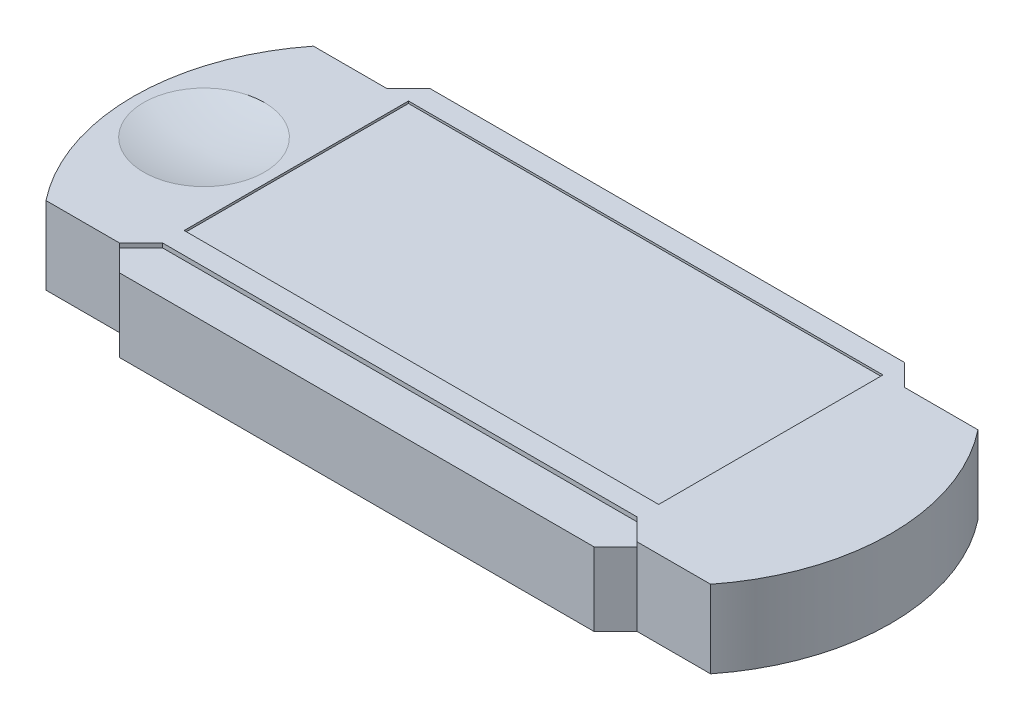
SolidWorks part; units mm, degrees
ref_plane "Front Plane" through (0, 0, 0) normal (0, 0, 1) x (1, 0, 0)
ref_plane "Top Plane" through (0, 0, 0) normal (0, 1, 0) x (1, 0, 0)
ref_plane "Right Plane" through (0, 0, 0) normal (1, 0, 0) x (0, 0, -1)
sketch "Sketch1" plane through (0, 0, 0) normal (0, 1, 0) x (1, 0, 0)
  line L0 (-87.8, 0) -> (87.8, 0) construction
  line L1 (-55, -36) -> (55, -36)
  line L2 (55, -36) -> (60, -31)
  line L3 (60, -31) -> (77.0301, -31)
  line L4 (0, 37.4833) -> (0, -47.1914) construction
  line L5 (60, 31) -> (77.0301, 31)
  line L6 (55, 36) -> (60, 31)
  line L7 (-55, 36) -> (55, 36)
  line L8 (-55, 36) -> (-60, 31)
  line L9 (-60, 31) -> (-77.0301, 31)
  line L10 (-60, -31) -> (-77.0301, -31)
  line L11 (-55, -36) -> (-60, -31)
  arc A0 (77.0301, -31) -> (77.0301, 31) centre (37.8, 0) ccw
  arc A1 (-77.0301, -31) -> (-77.0301, 31) centre (-37.8, 0) cw
  point P29 (0, 36)
  point P32 (0, -36)
  dimension "D5" = 50
  dimension "D1" = 72
  dimension "D2" = 62
  dimension "D3" = 110
  dimension "D4" = 45
  dimension "D6" = 75.6
extrude "Boss-Extrude1" add sketch "Sketch1" against normal blind 18
sketch "Sketch2" plane through (0, 0, 0) normal (0, 1, 0) x (1, 0, 0)
  line L0 (55, -36) -> (60, -31) construction
  line L1 (-55, -36) -> (55, -36) construction
  line L2 (-60, -31) -> (-55, -36) construction
  line L3 (55, -36) -> (60, -31)
  line L4 (-55, -36) -> (55, -36)
  line L5 (-60, -31) -> (-55, -36)
  line L6 (-60, -31) -> (60, -31) construction
  line L7 (-60, -31) -> (-55, -26)
  line L8 (-55, -26) -> (55, -26)
  line L9 (55, -26) -> (60, -31)
extrude "Cut-Extrude1" cut sketch "Sketch2" against normal blind 1
sketch "Sketch3" plane through (0, 0, 0) normal (0, 1, 0) x (1, 0, 0)
  line L0 (-60, 31) -> (-77.0301, 31) construction
  line L1 (-55, 31) -> (55, 31)
  line L2 (-55, 31) -> (-55, -21)
  line L3 (-55, -21) -> (55, -21)
  line L4 (55, 31) -> (55, -21)
  line L5 (-55, 31) -> (55, -21) construction
  line L6 (-55, -21) -> (55, 31) construction
  point P0 (0, 5)
  dimension "D1" = 52
  dimension "D2" = 110
extrude "Cut-Extrude2" cut sketch "Sketch3" against normal blind 0.5
sketch "Sketch4" plane through (0, 0, 0) normal (0, 0, 1) x (1, 0, 0)
  line L0 (-71.4, -2) -> (-71.4, 0) construction
  line L1 (-77.0301, 0) -> (-60, 0) construction
  line L2 (-71.4, 0) -> (-85.4, 0)
  line L3 (-77.0301, 0) -> (-87.8, 0) construction
  line L4 (-71.4, -2) -> (-71.4, 0)
  arc A0 (-85.4, 0) -> (-71.4, -2) centre (-70.6864, 52.9954) ccw
  point P10 (-71.4, -1)
  dimension "D4" = 55
  dimension "D1" = 14
  dimension "D2" = 2
  dimension "D3" = 71.4
revolve "Cut-Revolve1" cut sketch "Sketch4" angle 360 about L0
